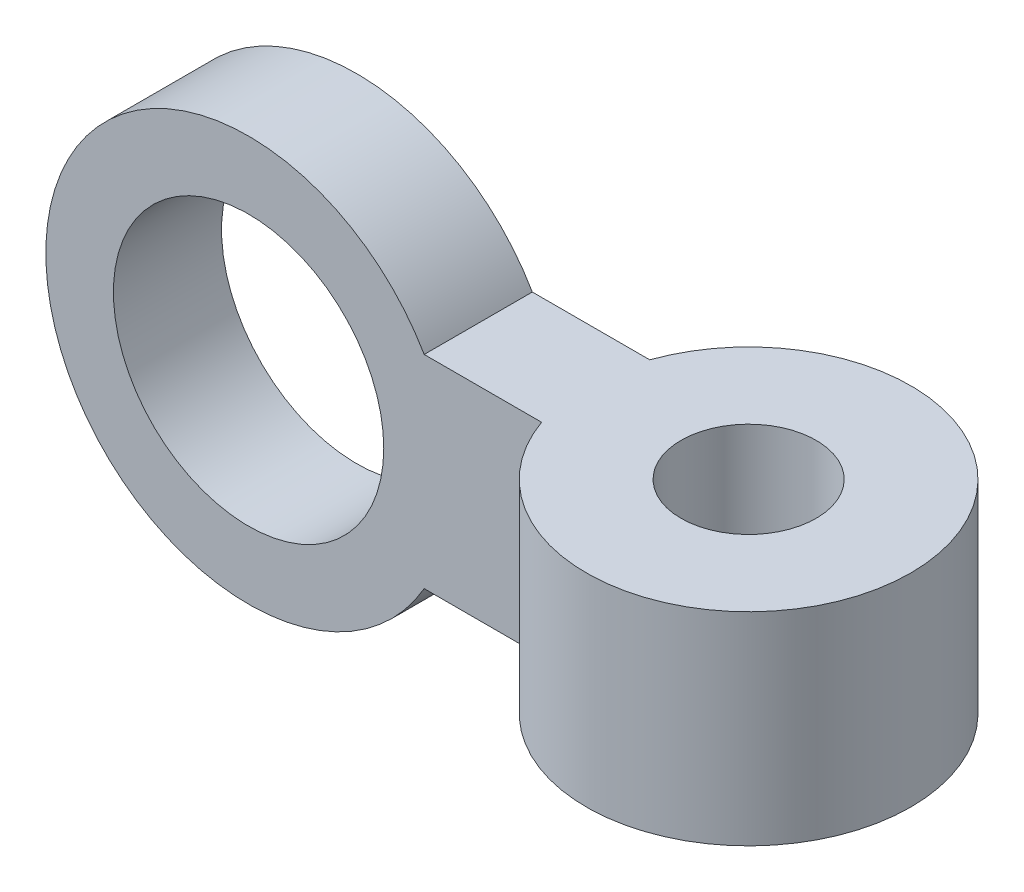
SolidWorks part; units mm, degrees
ref_plane "Front Plane" through (0, 0, 0) normal (0, 0, 1) x (1, 0, 0)
ref_plane "Top Plane" through (0, 0, 0) normal (0, 1, 0) x (1, 0, 0)
ref_plane "Right Plane" through (0, 0, 0) normal (1, 0, 0) x (0, 0, -1)
sketch "Sketch1" plane through (0, 0, 0) normal (0, 0, 1) x (1, 0, 0)
  line L0 (12.9904, 7.5) -> (32.9904, 7.5)
  line L1 (12.9904, -7.5) -> (32.9904, -7.5)
  line L2 (32.9904, -7.5) -> (32.9904, 7.5)
  circle A0 centre (0, 0) radius 10
  arc A1 (12.9904, 7.5) -> (12.9904, -7.5) centre (0, 0) ccw
  dimension "D1" = 20
  dimension "D2" = 30
  dimension "D3" = 7.5
  dimension "D4" = 7.5
  dimension "D5" = 20
extrude "Boss-Extrude1" add sketch "Sketch1" along normal blind 8
sketch "Sketch2" plane through (0, 7.5, 0) normal (0, 1, 0) x (1, 0, 0)
  line L0 (32.9904, -8) -> (32.9904, 0) construction
  line L1 (32.9904, 0) -> (12.9904, 0) construction
  line L2 (32.9904, -8) -> (12.9904, -8) construction
  line L3 (21.6767, 0) -> (32.9904, 0)
  line L4 (32.9904, 0) -> (32.9904, -8)
  line L5 (32.9904, -8) -> (21.6767, -8)
  line L7 (32.9904, 0) -> (12.9904, 0)
  line L8 (12.9904, 0) -> (12.9904, -8)
  line L9 (12.9904, -8) -> (32.9904, -8)
  line L10 (32.9904, -8) -> (32.9904, 0)
  line L11 (21.6767, 0) -> (12.9904, 0)
  line L12 (12.9904, 0) -> (12.9904, -8)
  line L13 (12.9904, -8) -> (21.6767, -8)
  arc A0 (21.6767, 0) -> (21.6767, -8) centre (32.9904, -4) cw
  line M5 (32.9904, 0) -> (12.9904, 0)
  line M7 (12.9904, -8) -> (32.9904, -8)
  line M8 (32.9904, -8) -> (32.9904, 0)
  dimension "D1" = 12
  dimension "D2" = 0
extrude "Boss-Extrude2" add sketch "Sketch2" against normal blind 15 contours A0 M5 M8 M7
sketch "Sketch3" plane through (0, 7.5, 0) normal (0, 1, 0) x (1, 0, 0)
  circle A0 centre (32.9904, -4) radius 5
  dimension "D1" = 10
extrude "Cut-Extrude1" cut sketch "Sketch3" against normal through all
